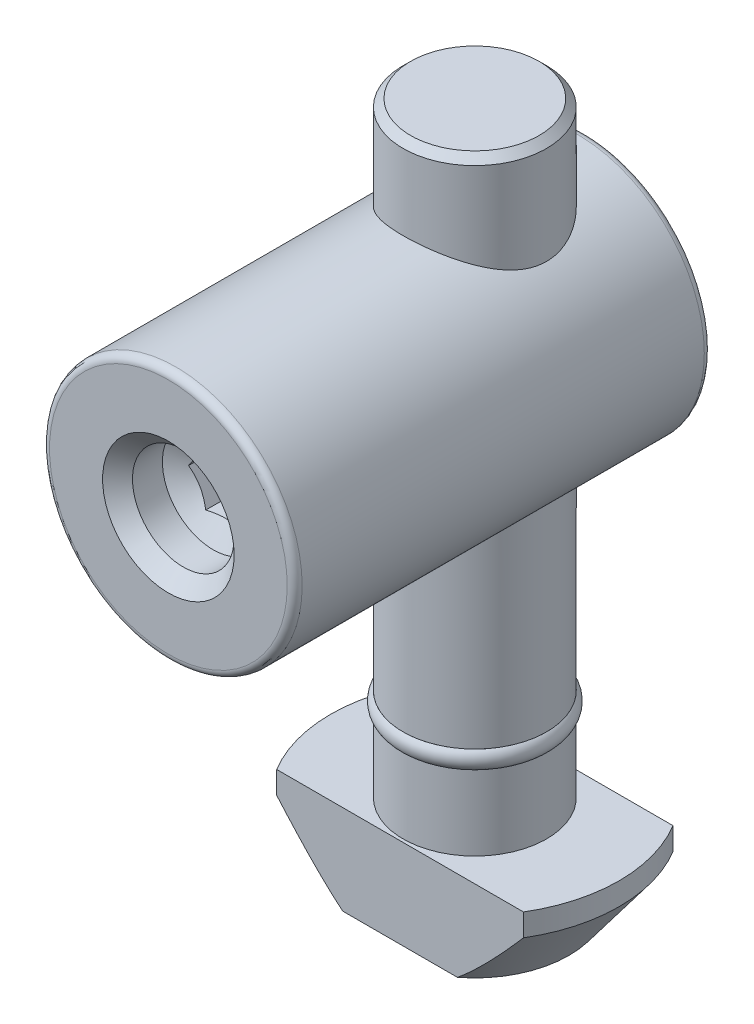
SolidWorks part; units mm, degrees
ref_plane "Спереди" through (0, 0, 0) normal (0, 0, 1) x (1, 0, 0)
ref_plane "Сверху" through (0, 0, 0) normal (0, 1, 0) x (1, 0, 0)
ref_plane "Справа" through (0, 0, 0) normal (1, 0, 0) x (0, 0, -1)
sketch "Эскиз3" plane through (0, 0, 0) normal (0, 0, 1) x (1, 0, 0)
  line L0 (0, 0) -> (-4.8, 0)
  line L1 (-4.8, 0) -> (-4.8, -34.3)
  line L2 (-4.8, -34.3) -> (-4.3, -34.3)
  line L3 (-4.3, -34.3) -> (-4.3, -35.5)
  line L4 (-4.3, -35.5) -> (-4.8, -35.5)
  line L5 (-4.8, -35.5) -> (-4.8, -40.5)
  line L7 (0, -46.5) -> (0, 0)
  line L8 (0, 0) -> (0, 5.384) construction
  line L9 (-4.8, -40.5) -> (-9.65, -40.5)
  line L10 (-9.65, -40.5) -> (-9.65, -42)
  line L11 (-9.65, -42) -> (-6.3, -46.5)
  line L12 (-6.3, -46.5) -> (0, -46.5)
  dimension "D1" = 9.6
  dimension "D2" = 1.2
  dimension "D3" = 46.5
  dimension "D4" = 0.5
  dimension "D5" = 5
  dimension "D6" = 6
  dimension "D7" = 1.5
  dimension "D8" = 1.5
  dimension "D9" = 19.3
revolve "Повернуть1" add sketch "Эскиз3" angle 360 about L8
sketch "Эскиз6" plane through (0, -46.5, 0) normal (0, -1, 0) x (1, 0, 0)
  line L1 (-9.65, -5) -> (9.65, -5)
  line L2 (-9.65, -5) -> (-9.65, 5)
  line L3 (-9.65, 5) -> (9.65, 5)
  line L4 (9.65, -5) -> (9.65, 5)
  line L5 (-9.65, -5) -> (9.65, 5) construction
  line L6 (-9.65, 5) -> (9.65, -5) construction
  circle A0 centre (0, 0) radius 9.65 construction
  point P0 (0, 0)
  point P6 (12.7212, 5.3537)
  dimension "D1" = 10
extrude "Вырез-Вытянуть1" cut sketch "Эскиз6" against normal up to surface (6 mm away) flip side to cut up to face at (0, -40.5, -9.65)
chamfer "Фаска1" distance 0.5 angle 45 1 edges at (0, 0, -4.8)
sketch "Эскиз12" plane through (0, 0, 0) normal (0, 0, 1) x (1, 0, 0)
  line L0 (4.3, 0) -> (-4.3, 0) construction
  circle A0 centre (0, -14) radius 8.45
  dimension "D1" = 16.9
  dimension "D2" = 14
extrude "Бобышка-Вытянуть2" add sketch "Эскиз12" along normal blind 20.5 and the other way blind 7.4
hole_wizard "Отверстие обработанное метчиком M81" positions "Эскиз13" profile "Эскиз14" tap size "M8" standard "ISO"
sketch "Эскиз13" plane through (0, 0, 20.5) normal (0, 0, 1) x (1, 0, 0)
  point P0 (0, -14)
cosmetic thread "Отверстие резьбы1" parameters "D1"=3, "D2"=8
sketch "Эскиз14" plane through (0, -14, 20.5) normal (1, 0, 0) x (0, -1, 0)
  line L0 (0, 0) -> (0, 5.0429)
  line L1 (0, 5.0429) -> (3.4, 3)
  line L2 (3.4, 3) -> (3.4, 1)
  line L3 (3.4, 1) -> (4.4, 0)
  line L5 (4.4, 0) -> (0, 0)
  line L6 (-3.4, 1) -> (-4.4, 0) construction
  line L10 (0, 5.0429) -> (-3.4, 3) construction
  line L11 (0, -6.35) -> (0, 107.95) construction
  dimension "Диаметр сверла" = 6.8
  dimension "Глубина сверла" = 3
  dimension "Диаметр передней зенковки" = 8.8
  dimension "Угол передней зенковки" = 90
  dimension "Угол заточки сверла" = 118
fillet "Скругление1" radius 0.5 2 edges at (8.45, -14, -7.4) (8.45, -14, 20.5)
sketch "Эскиз15" plane through (0, 0, 20.5) normal (0, 0, 1) x (1, 0, 0)
  line L1 (2.3094, -14) -> (1.1547, -12)
  line L2 (1.1547, -12) -> (-1.1547, -12)
  line L3 (-1.1547, -12) -> (-2.3094, -14)
  line L4 (-2.3094, -14) -> (-1.1547, -16)
  line L5 (-1.1547, -16) -> (1.1547, -16)
  line L6 (1.1547, -16) -> (2.3094, -14)
  circle A0 centre (0, -14) radius 2 construction
  dimension "D1" = 4
extrude "Вырез-Вытянуть2" cut sketch "Эскиз15" against normal blind 6
sketch "Эскиз16" plane through (0, 0, 0) normal (0, 0, 1) x (1, 0, 0)
  line L0 (-4.3, -34.3) -> (-4.8, -34.3)
  line L1 (-4.3, -34.3) -> (-4.3, -35.5) construction
  line L2 (-4.8, -35.5) -> (-4.3, -35.5)
  line L3 (-4.3, -35.5) -> (-4.3, -34.3)
  line L4 (-4.3, -34.3) -> (4.3, -34.3) construction
  line L7 (-4.8, -20.9543) -> (-4.8, -34.3) construction
  line L8 (4.8, -35.5) -> (-4.8, -35.5) construction
  line L9 (0, -34.3) -> (0, -35.5) construction
  arc A0 (-4.8, -34.3) -> (-4.8, -35.5) centre (-4.3, -34.9) ccw
  point P15 (-4.3, -34.9)
revolve "Повернуть2" add sketch "Эскиз16" angle 360 about L9
